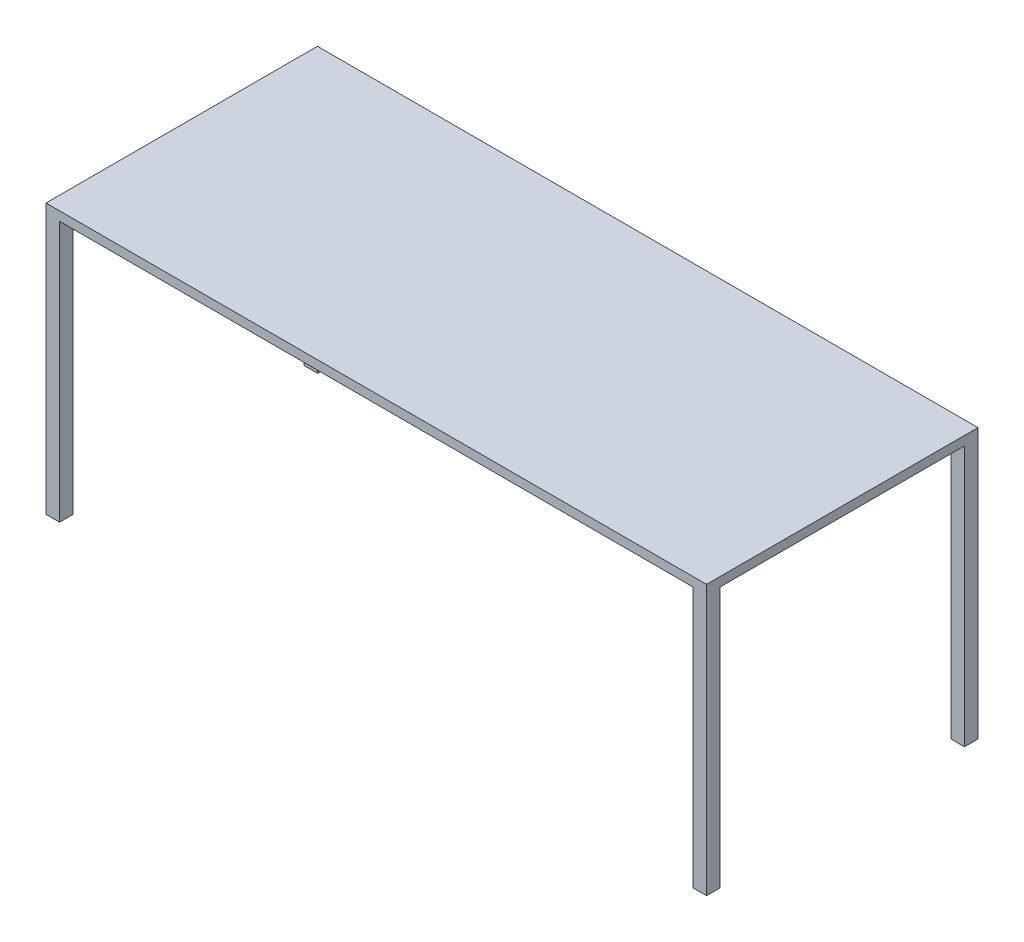
SolidWorks part; units mm, degrees
ref_plane "Front Plane" through (0, 0, 0) normal (0, 0, 1) x (1, 0, 0)
ref_plane "Top Plane" through (0, 0, 0) normal (0, 1, 0) x (1, 0, 0)
ref_plane "Right Plane" through (0, 0, 0) normal (1, 0, 0) x (0, 0, -1)
sketch "Sketch1" plane through (0, 0, 0) normal (0, 1, 0) x (1, 0, 0)
  line L1 (927.1, -381) -> (-927.1, -381)
  line L2 (927.1, -381) -> (927.1, 381)
  line L3 (927.1, 381) -> (-927.1, 381)
  line L4 (-927.1, -381) -> (-927.1, 381)
  line L5 (927.1, -381) -> (-927.1, 381) construction
  line L6 (927.1, 381) -> (-927.1, -381) construction
  point P0 (0, 0)
  dimension "D1" = 1854.2
  dimension "D2" = 762
extrude "Boss-Extrude1" add sketch "Sketch1" along normal blind 756.92
sketch "Sketch2" plane through (0, 0, 0) normal (0, -1, 0) x (1, 0, 0)
  line L0 (-927.1, 381) -> (927.1, 381) construction
  line L1 (-889, 381) -> (889, 381)
  line L2 (-889, 381) -> (-889, 342.9)
  line L3 (-889, -381) -> (889, -381)
  line L4 (889, 381) -> (889, 342.9)
  line L5 (927.1, -381) -> (-927.1, -381) construction
  line L6 (-927.1, -381) -> (-927.1, 381) construction
  line L7 (-927.1, 342.9) -> (-889, 342.9)
  line L8 (-927.1, 342.9) -> (-927.1, -342.9)
  line L9 (-927.1, -342.9) -> (-889, -342.9)
  line L10 (927.1, 342.9) -> (927.1, -342.9)
  line L11 (927.1, 381) -> (927.1, -381) construction
  line L12 (-889, -342.9) -> (-889, -381)
  line L13 (889, 342.9) -> (927.1, 342.9)
  line L14 (889, -342.9) -> (927.1, -342.9)
  line L15 (889, -342.9) -> (889, -381)
  dimension "D1" = 38.1
  dimension "D2" = 38.1
  dimension "D3" = 38.1
  dimension "D4" = 38.1
extrude "Cut-Extrude1" cut sketch "Sketch2" against normal blind 731.52
